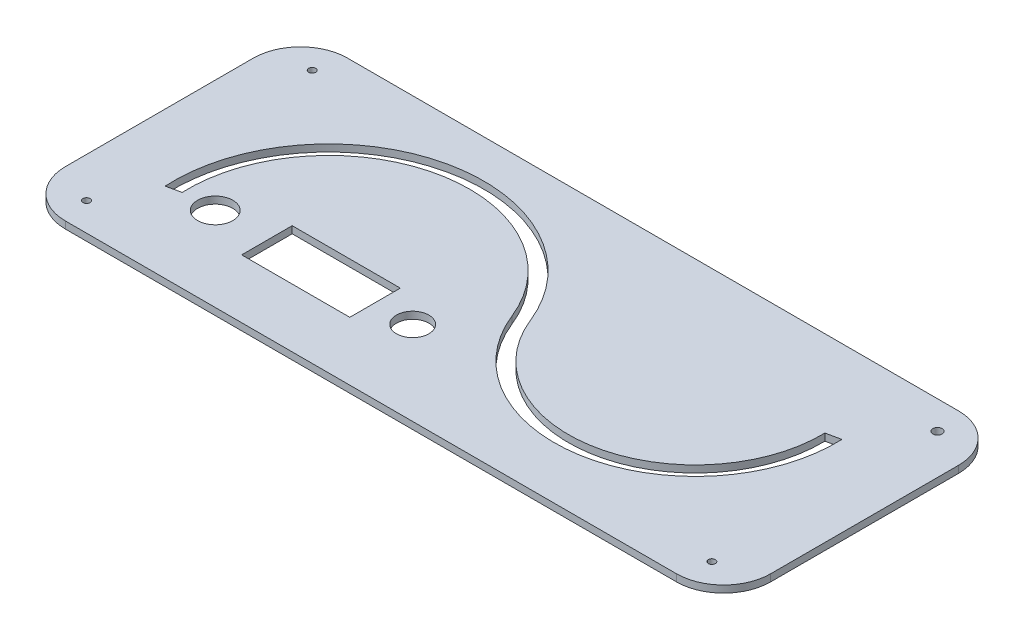
SolidWorks part; units mm, degrees
ref_plane "Спереди" through (0, 0, 0) normal (0, 0, 1) x (1, 0, 0)
ref_plane "Сверху" through (0, 0, 0) normal (0, 1, 0) x (1, 0, 0)
ref_plane "Справа" through (0, 0, 0) normal (1, 0, 0) x (0, 0, -1)
sketch "Эскиз2" plane through (0, 0, 0) normal (0, 1, 0) x (1, 0, 0)
  line L0 (-300, 0) -> (0, 120) construction
  line L1 (0, 0) -> (-300, 0)
  line L2 (0, 0) -> (0, 120)
  line L3 (0, 120) -> (-300, 120)
  line L4 (-300, 0) -> (-300, 120)
  line L6 (-300, 120) -> (0, 0) construction
  line L7 (-300, 28) -> (0, 92) construction
  line L8 (-271.6071, 34.0572) -> (-265.6609, 35.3257)
  line L10 (-40.303, 83.402) -> (-34.3391, 84.6743)
  line L11 (0, 60) -> (-300, 60) construction
  line L12 (-150, 120) -> (-150, 0) construction
  line L14 (-230, 46.4965) -> (-184, 46.4965)
  line L15 (-230, 46.4965) -> (-230, 24.9965)
  line L16 (-230, 24.9965) -> (-184, 24.9965)
  line L17 (-184, 46.4965) -> (-184, 24.9965)
  line L18 (-230, 46.4965) -> (-184, 24.9965) construction
  line L19 (-230, 24.9965) -> (-184, 46.4965) construction
  circle A0 centre (-283, 108) radius 1.5
  circle A1 centre (-17, 108) radius 2
  circle A2 centre (-17, 12) radius 1.5
  circle A3 centre (-283, 12) radius 1.5
  arc A4 (-150, 60) -> (-265.6609, 35.3257) centre (-205.7086, 37.7166) ccw
  arc A5 (-150, 60) -> (-34.3391, 84.6743) centre (-94.2914, 82.2834) ccw
  arc A8 (-144.4291, 62.2283) -> (-271.6071, 34.0572) centre (-205.7086, 37.7166) ccw
  arc A9 (-144.4291, 62.2283) -> (-40.303, 83.402) centre (-94.2914, 82.2834) ccw
  circle A12 centre (-168, 35.7465) radius 6.9
  circle A14 centre (-252, 35.7465) radius 7.5
  point P18 (-150, 60)
  point P20 (-300, 28)
  point P21 (0, 92)
  point P25 (-207, 35.7465)
  dimension "D5" = 3
  dimension "D6" = 4
  dimension "D7" = 3
  dimension "D8" = 3
  dimension "D17" = 132
  dimension "D18" = 46
  dimension "D15" = 120
  dimension "D16" = 120
  dimension "D21" = 21.5
  dimension "D22" = 24.9965
  dimension "D23" = 13.8
  dimension "D24" = 39
  dimension "D25" = 15
  dimension "D1" = 300
  dimension "D2" = 120
  dimension "D3" = 266
  dimension "D4" = 96
  dimension "D9" = 266
  dimension "D10" = 12
  dimension "D11" = 17
  dimension "D12" = 96
  dimension "D13" = 17
  dimension "D14" = 12
  dimension "D19" = 28
  dimension "D20" = 28
  dimension "D26" = 45
  dimension "59" = 70
extrude "Бобышка-Вытянуть2" add sketch "Эскиз2" along normal blind 3
fillet "Скругление1" radius 20 4 edges at (0, 1.5, 0) (0, 1.5, -120) (-300, 1.5, -120) (-300, 1.5, 0)
